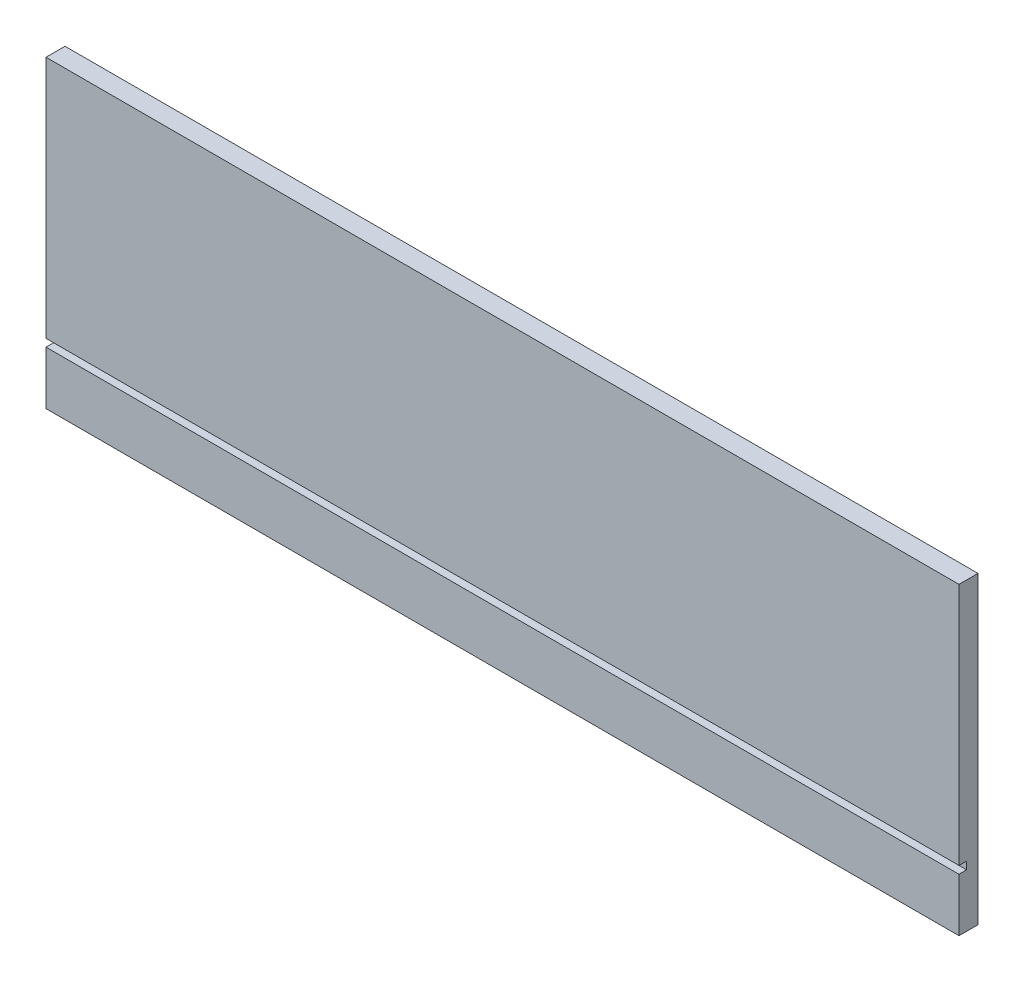
SolidWorks part; units mm, degrees
ref_plane "Front Plane" through (0, 0, 0) normal (0, 0, 1) x (1, 0, 0)
ref_plane "Top Plane" through (0, 0, 0) normal (0, 1, 0) x (1, 0, 0)
ref_plane "Right Plane" through (0, 0, 0) normal (1, 0, 0) x (0, 0, -1)
sketch "Sketch1" plane through (0, 0, 0) normal (0, 0, 1) x (1, 0, 0)
  line L1 (0, 0) -> (762, 0)
  line L2 (0, 0) -> (0, 254)
  line L3 (0, 254) -> (762, 254)
  line L4 (762, 0) -> (762, 254)
  dimension "D1" = 762
  dimension "D2" = 254
extrude "Boss-Extrude1" add sketch "Sketch1" along normal blind 15.875
sketch "Sketch2" plane through (762, 0, 0) normal (1, 0, 0) x (0, 0, -1)
  line L0 (-15.875, 0) -> (-15.875, 254) construction
  line L1 (-15.875, 50.8) -> (-9.525, 50.8)
  line L2 (-15.875, 50.8) -> (-15.875, 44.45)
  line L3 (-15.875, 44.45) -> (-9.525, 44.45)
  line L4 (-9.525, 50.8) -> (-9.525, 44.45)
  dimension "D1" = 6.35
  dimension "D2" = 6.35
  dimension "D3" = 203.2
extrude "Cut-Extrude1" cut sketch "Sketch2" against normal through all
